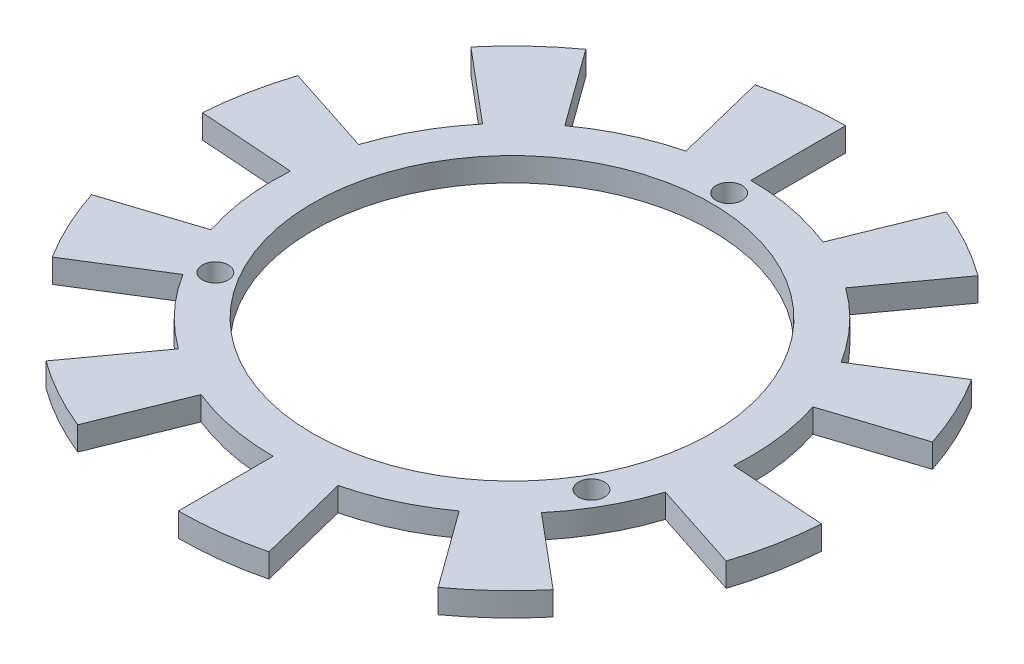
SolidWorks part; units mm, degrees
material "AISI 1010 Steel, hot rolled bar"
ref_plane "Front Plane" through (0, 0, 0) normal (0, 0, 1) x (1, 0, 0)
ref_plane "Top Plane" through (0, 0, 0) normal (0, 1, 0) x (1, 0, 0)
ref_plane "Right Plane" through (0, 0, 0) normal (1, 0, 0) x (0, 0, -1)
sketch "Sketch1" plane through (0, 0, 0) normal (0, 1, 0) x (1, 0, 0)
  circle A0 centre (0, 0) radius 25.25
  dimension "D1" = 50.5
extrude "Extrude-Thin1" add sketch "Sketch1" against normal blind 3 thin
sketch "Sketch2" plane through (0, 0, 0) normal (0, 1, 0) x (1, 0, 0)
  line L0 (0, -30.25) -> (0, 30.25) construction
  line L1 (0, 0) -> (23.8157, -13.75) construction
  line L2 (0, 0) -> (-23.8157, -13.75) construction
  circle A0 centre (0, 27.5) radius 1.65
  circle A1 centre (0, 0) radius 30.25 construction
  circle A4 centre (0, 0) radius 27.5 construction
  circle A7 centre (23.8157, -13.75) radius 1.65
  circle A8 centre (-23.8157, -13.75) radius 1.65
  dimension "D1" = 55
  dimension "D2" = 3.3
  dimension "D3" = 120
  dimension "D4" = 120
extrude "Cut-Extrude3" cut sketch "Sketch2" against normal blind 10
sketch "Sketch5" plane through (0, -3, 0) normal (0, -1, 0) x (1, 0, 0)
  line L0 (0, 0) -> (0, 35.9971) construction
  line L1 (0, 0) -> (8.2512, 33.0937) construction
  line L2 (0, 42.25) -> (0, 30.25)
  line L3 (7.3181, 29.3514) -> (10.2212, 40.995)
  line L4 (24.8339, 34.181) -> (17.7805, 24.4728)
  line L5 (23.1728, 19.4443) -> (32.3654, 27.1578)
  line L6 (40.1821, 13.056) -> (28.7695, 9.3478)
  line L7 (30.1763, 2.1101) -> (42.1471, 2.9472)
  line L8 (40.1821, -13.056) -> (28.7695, -9.3478)
  line L9 (25.6535, -16.0301) -> (35.83, -22.3891)
  line L10 (24.8339, -34.181) -> (17.7805, -24.4728)
  line L11 (11.3318, -28.0473) -> (15.8271, -39.1735)
  line L12 (0, -42.25) -> (0, -30.25)
  line L13 (-7.3181, -29.3514) -> (-10.2212, -40.995)
  line L14 (-24.8339, -34.181) -> (-17.7805, -24.4728)
  line L15 (-23.1728, -19.4443) -> (-32.3654, -27.1578)
  line L16 (-40.1821, -13.056) -> (-28.7695, -9.3478)
  line L17 (-30.1763, -2.1101) -> (-42.1471, -2.9472)
  line L18 (-40.1821, 13.056) -> (-28.7695, 9.3478)
  line L19 (-25.6535, 16.0301) -> (-35.83, 22.3891)
  line L20 (-24.8339, 34.181) -> (-17.7805, 24.4728)
  line L21 (-11.3318, 28.0473) -> (-15.8271, 39.1735)
  circle A0 centre (0, 0) radius 30.25 construction
  arc A1 (7.3181, 29.3514) -> (0, 30.25) centre (0, 0) ccw
  arc A2 (10.2212, 40.995) -> (0, 42.25) centre (0, 0) ccw
  arc A3 (32.3654, 27.1578) -> (24.8339, 34.181) centre (0, 0) ccw
  arc A4 (23.1728, 19.4443) -> (17.7805, 24.4728) centre (0, 0) ccw
  arc A5 (42.1471, 2.9472) -> (40.1821, 13.056) centre (0, 0) ccw
  arc A6 (30.1763, 2.1101) -> (28.7695, 9.3478) centre (0, 0) ccw
  arc A7 (35.83, -22.3891) -> (40.1821, -13.056) centre (0, 0) ccw
  arc A8 (25.6535, -16.0301) -> (28.7695, -9.3478) centre (0, 0) ccw
  arc A9 (15.8271, -39.1735) -> (24.8339, -34.181) centre (0, 0) ccw
  arc A10 (11.3318, -28.0473) -> (17.7805, -24.4728) centre (0, 0) ccw
  arc A11 (-10.2212, -40.995) -> (0, -42.25) centre (0, 0) ccw
  arc A12 (-7.3181, -29.3514) -> (0, -30.25) centre (0, 0) ccw
  arc A13 (-32.3654, -27.1578) -> (-24.8339, -34.181) centre (0, 0) ccw
  arc A14 (-23.1728, -19.4443) -> (-17.7805, -24.4728) centre (0, 0) ccw
  arc A15 (-42.1471, -2.9472) -> (-40.1821, -13.056) centre (0, 0) ccw
  arc A16 (-30.1763, -2.1101) -> (-28.7695, -9.3478) centre (0, 0) ccw
  arc A17 (-35.83, 22.3891) -> (-40.1821, 13.056) centre (0, 0) ccw
  arc A18 (-25.6535, 16.0301) -> (-28.7695, 9.3478) centre (0, 0) ccw
  arc A19 (-15.8271, 39.1735) -> (-24.8339, 34.181) centre (0, 0) ccw
  arc A20 (-11.3318, 28.0473) -> (-17.7805, 24.4728) centre (0, 0) ccw
  point P87 (0, 0)
  dimension "D2" = 12
  dimension "D1" = 14
  dimension "D3" = 10
extrude "Boss-Extrude1" add sketch "Sketch5" against normal blind 3
